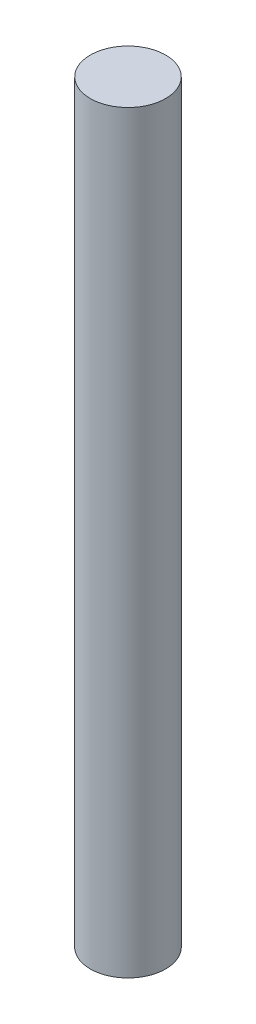
SolidWorks part; units mm, degrees
ref_plane "Front Plane" through (0, 0, 0) normal (0, 0, 1) x (1, 0, 0)
ref_plane "Top Plane" through (0, 0, 0) normal (0, 1, 0) x (1, 0, 0)
ref_plane "Right Plane" through (0, 0, 0) normal (1, 0, 0) x (0, 0, -1)
sketch "Sketch1" plane through (0, 0, 0) normal (0, 1, 0) x (1, 0, 0)
  circle A0 centre (0, 0) radius 7.5
  dimension "D1" = 15
extrude "Boss-Extrude1" add sketch "Sketch1" along normal blind 150
